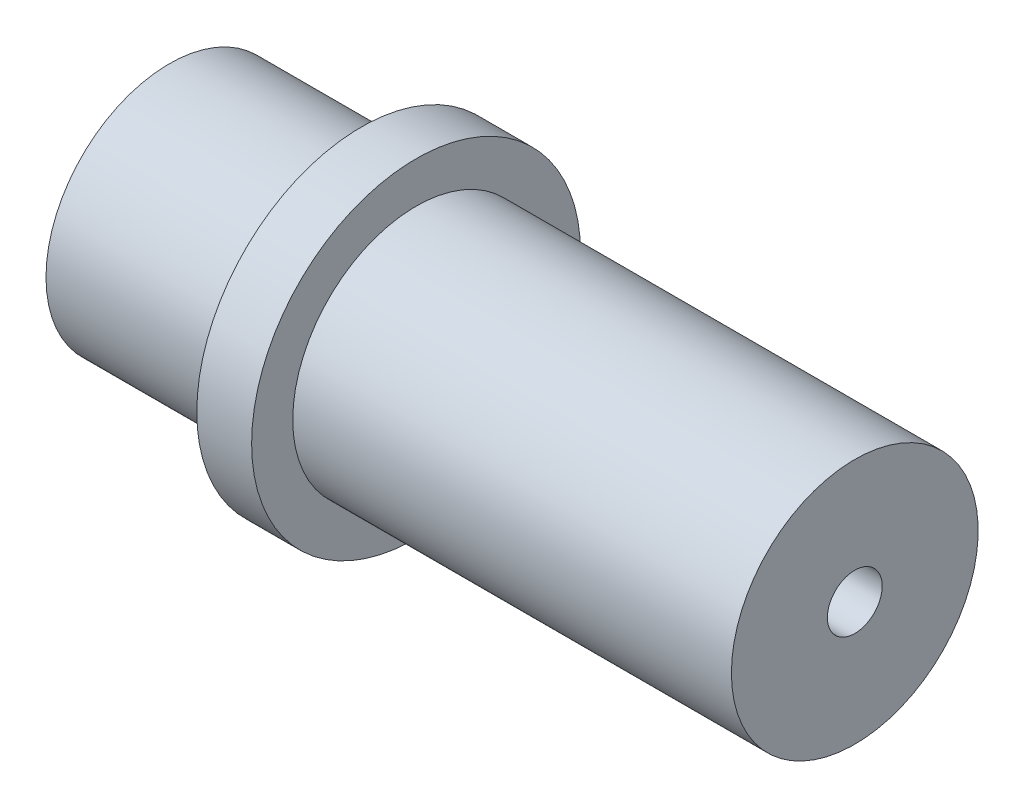
SolidWorks part; units mm, degrees
ref_plane "Front Plane" through (0, 0, 0) normal (0, 0, 1) x (1, 0, 0)
ref_plane "Top Plane" through (0, 0, 0) normal (0, 1, 0) x (1, 0, 0)
ref_plane "Right Plane" through (0, 0, 0) normal (1, 0, 0) x (0, 0, -1)
sketch "Sketch2" plane through (0, 0, 0) normal (0, 1, 0) x (1, 0, 0)
  line L0 (-15.625, 0) -> (15.625, 0) construction
  line L1 (-15.625, 0) -> (-15.625, 5.625)
  line L2 (-15.625, 5.625) -> (-6.875, 5.625)
  line L3 (-6.875, 0) -> (-6.875, 7.5)
  line L4 (-6.875, 7.5) -> (-4.375, 7.5)
  line L5 (-4.375, 7.5) -> (-4.375, 0)
  line L6 (-4.375, 5.625) -> (15.625, 5.625)
  line L7 (15.625, 5.625) -> (15.625, 0)
  point P4 (0, 0)
revolve "Revolve1" add sketch "Sketch2" angle 360 about L0
sketch "Sketch3" plane through (-15.625, 0, 0) normal (-1, 0, 0) x (0, 0, 1)
  circle A0 centre (0, 0) radius 1.25
extrude "Cut-Extrude1" cut sketch "Sketch3" against normal blind 31.25
sketch "Sketch4" plane through (-15.625, 0, 0) normal (-1, 0, 0) x (0, 0, 1)
  circle A0 centre (0, 0) radius 1.875
extrude "Cut-Extrude2" cut sketch "Sketch4" against normal blind 21.75
